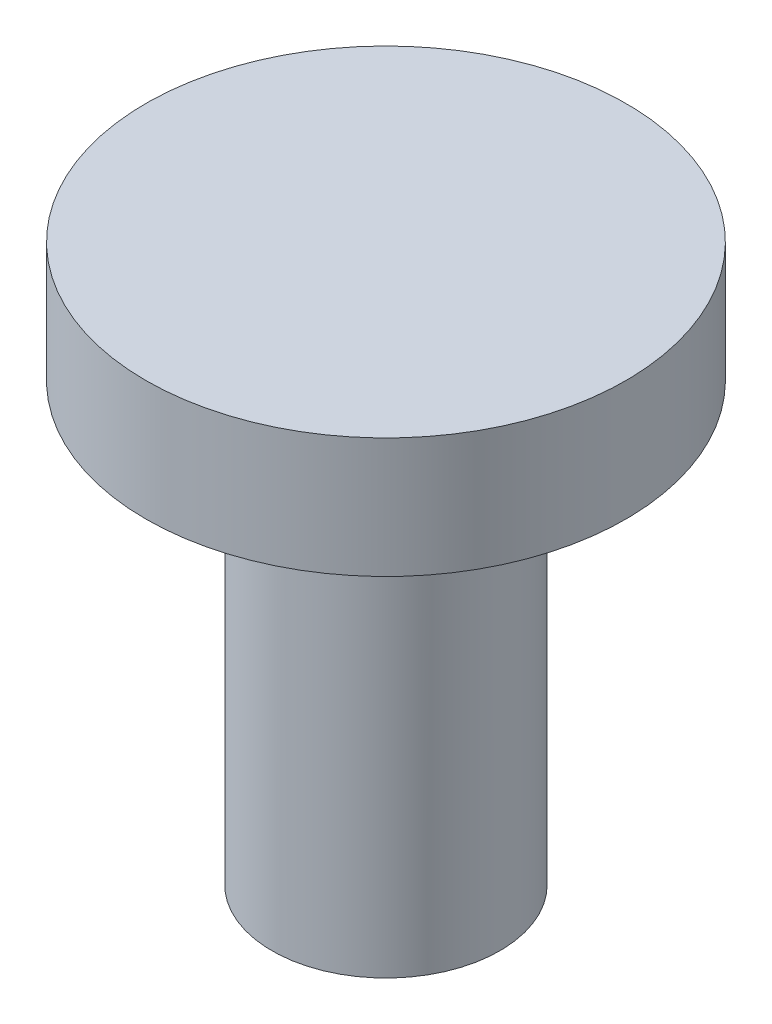
SolidWorks part; units mm, degrees
ref_plane "Front Plane" through (0, 0, 0) normal (0, 0, 1) x (1, 0, 0)
ref_plane "Top Plane" through (0, 0, 0) normal (0, 1, 0) x (1, 0, 0)
ref_plane "Right Plane" through (0, 0, 0) normal (1, 0, 0) x (0, 0, -1)
sketch "Sketch1" plane through (0, 0, 0) normal (0, 1, 0) x (1, 0, 0)
  circle A0 centre (0, 0) radius 4.75
extrude "Boss-Extrude1" add sketch "Sketch1" along normal blind 10
sketch "Sketch2" plane through (0, 10, 0) normal (0, 1, 0) x (1, 0, 0)
  circle A0 centre (0, 0) radius 10
extrude "Boss-Extrude2" add sketch "Sketch2" along normal blind 5
sketch "Sketch3" plane through (0, 0, 0) normal (0, -1, 0) x (1, 0, 0)
  circle A0 centre (0, 0) radius 4.75
extrude "Boss-Extrude3" add sketch "Sketch3" along normal blind 13.2
sketch "Sketch4" plane through (0, -13.2, 0) normal (0, -1, 0) x (1, 0, 0)
  circle A0 centre (0, 0) radius 4.75
extrude "Cut-Extrude1" cut sketch "Sketch4" against normal blind 5
